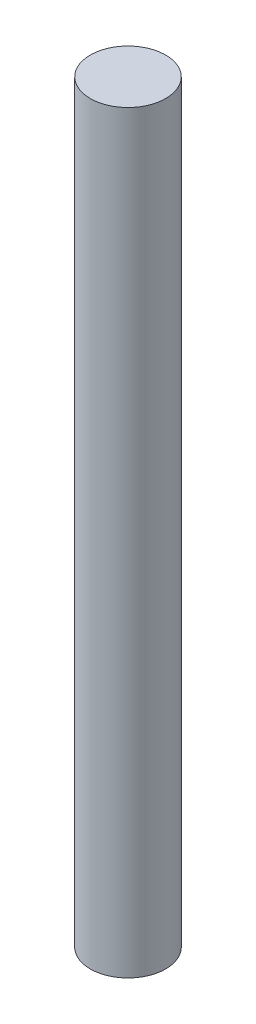
SolidWorks part; units mm, degrees
ref_plane "Front Plane" through (0, 0, 0) normal (0, 0, 1) x (1, 0, 0)
ref_plane "Top Plane" through (0, 0, 0) normal (0, 1, 0) x (1, 0, 0)
ref_plane "Right Plane" through (0, 0, 0) normal (1, 0, 0) x (0, 0, -1)
sketch "Sketch1" plane through (0, 0, 0) normal (0, 1, 0) x (1, 0, 0)
  circle A0 centre (0, 0) radius 75
  dimension "D1" = 150
extrude "Boss-Extrude1" add sketch "Sketch1" along normal blind 1500 contours A0
sketch3d "URDF Reference"
  line L0 (0, 0, 0) -> (10, 0, 0) construction
  line L1 (0, 0, 0) -> (0, 0, -10) construction
  point P0 (0, 0, 0)
  point P1 (0, 0, 0)
